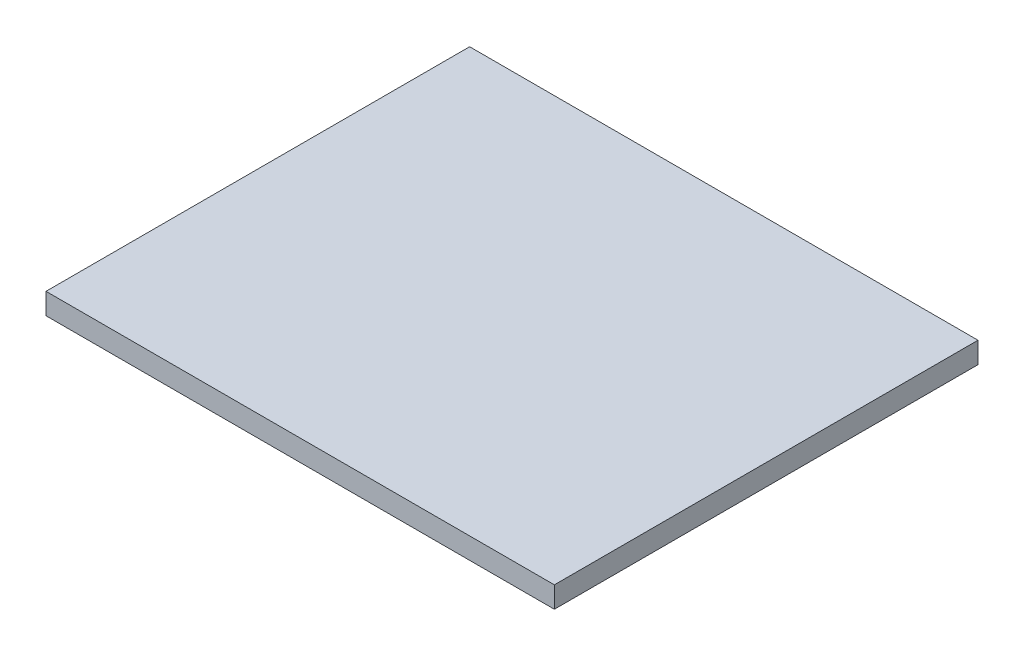
SolidWorks part; units mm, degrees
ref_plane "Front Plane" through (0, 0, 0) normal (0, 0, 1) x (1, 0, 0)
ref_plane "Top Plane" through (0, 0, 0) normal (0, 1, 0) x (1, 0, 0)
ref_plane "Right Plane" through (0, 0, 0) normal (1, 0, 0) x (0, 0, -1)
sketch "Sketch1" plane through (0, 0, 0) normal (0, 1, 0) x (1, 0, 0)
  line L1 (-76.2, -63.5) -> (76.2, -63.5)
  line L2 (-76.2, -63.5) -> (-76.2, 63.5)
  line L3 (-76.2, 63.5) -> (76.2, 63.5)
  line L4 (76.2, -63.5) -> (76.2, 63.5)
  line L5 (-76.2, -63.5) -> (76.2, 63.5) construction
  line L6 (-76.2, 63.5) -> (76.2, -63.5) construction
  point P0 (0, 0)
  dimension "D1" = 152.4
  dimension "D2" = 127
extrude "Boss-Extrude1" add sketch "Sketch1" along normal blind 6.35
sketch "Sketch2" plane through (0, 0, 0) normal (0, 1, 0) x (1, 0, 0)
  line L0 (0, 63.5) -> (0, -63.5) construction
  line L1 (76.2, 63.5) -> (-76.2, 63.5) construction
  line L2 (-76.2, -63.5) -> (76.2, -63.5) construction
  line L3 (0, 0) -> (-76.2, 0) construction
  line L4 (-76.2, 63.5) -> (-76.2, -63.5) construction
  line L5 (0, 0) -> (76.2, 0) construction
  line L6 (76.2, -63.5) -> (76.2, 63.5) construction
  line L7 (-76.2, 63.5) -> (-76.2, 57.15)
  line L8 (-76.2, -63.5) -> (-50.8, -63.5)
  line L9 (-76.2, -63.5) -> (-76.2, -57.15)
  line L10 (-76.2, -57.15) -> (-50.8, -57.15)
  line L11 (-50.8, -63.5) -> (-50.8, -57.15)
  line L12 (-76.2, 63.5) -> (-50.8, 63.5)
  line L13 (-50.8, 63.5) -> (-50.8, 57.15)
  line L14 (-76.2, 57.15) -> (-50.8, 57.15)
  line L15 (50.8, -63.5) -> (50.8, -57.15)
  line L16 (76.2, -63.5) -> (50.8, -63.5)
  line L17 (76.2, -63.5) -> (76.2, -57.15)
  line L18 (76.2, -57.15) -> (50.8, -57.15)
  line L19 (76.2, 63.5) -> (76.2, 57.15)
  line L20 (76.2, 63.5) -> (50.8, 63.5)
  line L21 (50.8, 63.5) -> (50.8, 57.15)
  line L22 (76.2, 57.15) -> (50.8, 57.15)
  line L23 (69.85, -50.8) -> (63.5, -50.8)
  line L24 (-69.85, 50.8) -> (-63.5, 50.8)
  line L25 (-69.85, 50.8) -> (-69.85, -50.8)
  line L26 (-69.85, -50.8) -> (-63.5, -50.8)
  line L27 (-63.5, 50.8) -> (-63.5, -50.8)
  line L28 (69.85, 50.8) -> (69.85, -50.8)
  line L29 (63.5, 50.8) -> (63.5, -50.8)
  line L30 (69.85, 50.8) -> (63.5, 50.8)
  point P35 (-66.675, -50.8)
  dimension "D1" = 6.35
  dimension "D2" = 25.4
  dimension "D3" = 6.35
  dimension "D4" = 12.7
  dimension "D5" = 12.7
  dimension "D6" = 6.35
